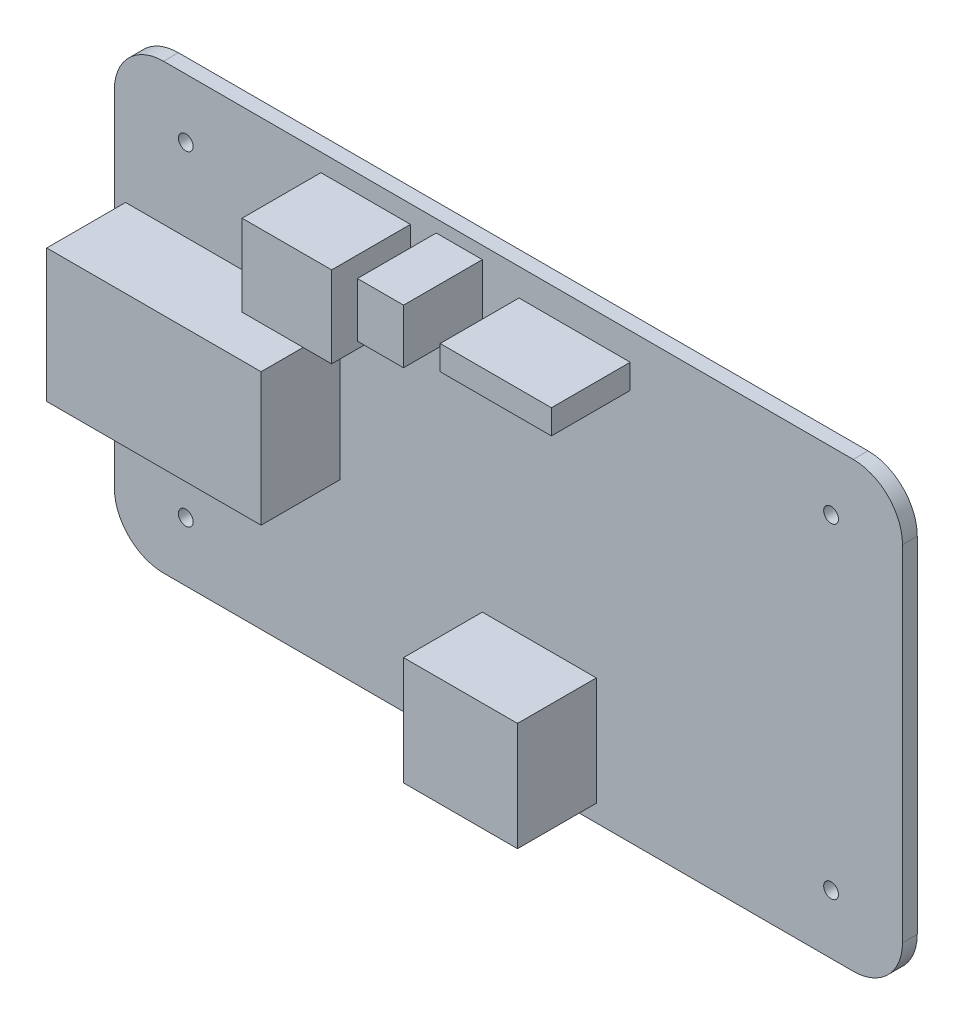
SolidWorks part; units mm, degrees
ref_plane "Front Plane" through (0, 0, 0) normal (0, 0, 1) x (1, 0, 0)
ref_plane "Top Plane" through (0, 0, 0) normal (0, 1, 0) x (1, 0, 0)
ref_plane "Right Plane" through (0, 0, 0) normal (1, 0, 0) x (0, 0, -1)
sketch "Sketch1" plane through (0, 0, 0) normal (0, 0, 1) x (1, 0, 0)
  line L1 (-80, 45) -> (80, 45)
  line L2 (-80, 45) -> (-80, -45)
  line L3 (-80, -45) -> (80, -45)
  line L4 (80, 45) -> (80, -45)
  line L5 (-80, 45) -> (80, -45) construction
  line L6 (-80, -45) -> (80, 45) construction
  point P0 (0, 0)
  dimension "D1" = 90
  dimension "D2" = 160
extrude "Boss-Extrude1" add sketch "Sketch1" along normal blind 3
fillet "Fillet1" radius 10 4 edges at (-80, -45, 1.5) (80, -45, 1.5) (80, 45, 1.5) (-80, 45, 1.5)
sketch "Sketch2" plane through (0, 0, 3) normal (0, 0, 1) x (1, 0, 0)
  line L5 (-65.5, 33) -> (65.5, -33) construction
  line L6 (-65.5, -33) -> (65.5, 33) construction
  circle A0 centre (-65.5, 33) radius 1.5
  circle A1 centre (65.5, 33) radius 1.5
  circle A2 centre (65.5, -33) radius 1.5
  circle A3 centre (-65.5, -33) radius 1.5
  point P0 (0, 0)
  dimension "D3" = 3
  dimension "D4" = 3
  dimension "D5" = 3
  dimension "D6" = 3
  dimension "D1" = 131
  dimension "D2" = 66
extrude "Cut-Extrude1" cut sketch "Sketch2" against normal through all
sketch "Sketch3" plane through (0, 0, 3) normal (0, 0, 1) x (1, 0, 0)
  line L1 (-77.7255, 16.3109) -> (-34.2096, 16.3109)
  line L2 (-77.7255, 16.3109) -> (-77.7255, -10.68)
  line L3 (-77.7255, -10.68) -> (-34.2096, -10.68)
  line L4 (-34.2096, 16.3109) -> (-34.2096, -10.68)
  line L5 (-77.7255, 16.3109) -> (-34.2096, -10.68) construction
  line L6 (-77.7255, -10.68) -> (-34.2096, 16.3109) construction
  line L7 (-5.2908, -19.4933) -> (17.8443, -19.4933)
  line L8 (-5.2908, -19.4933) -> (-5.2908, -41.5267)
  line L9 (-5.2908, -41.5267) -> (17.8443, -41.5267)
  line L10 (17.8443, -19.4933) -> (17.8443, -41.5267)
  line L11 (-5.2908, -19.4933) -> (17.8443, -41.5267) construction
  line L12 (-5.2908, -41.5267) -> (17.8443, -19.4933) construction
  line L13 (-38.0654, 41.3739) -> (-19.8879, 41.3739)
  line L14 (-38.0654, 41.3739) -> (-38.0654, 24.8489)
  line L15 (-38.0654, 24.8489) -> (-19.8879, 24.8489)
  line L16 (-19.8879, 41.3739) -> (-19.8879, 24.8489)
  line L17 (-38.0654, 41.3739) -> (-19.8879, 24.8489) construction
  line L18 (-38.0654, 24.8489) -> (-19.8879, 41.3739) construction
  line L19 (-14.655, 42.4756) -> (-5.2908, 42.4756)
  line L20 (-14.655, 42.4756) -> (-14.655, 31.4589)
  line L21 (-14.655, 31.4589) -> (-5.2908, 31.4589)
  line L22 (-5.2908, 42.4756) -> (-5.2908, 31.4589)
  line L23 (-14.655, 42.4756) -> (-5.2908, 31.4589) construction
  line L24 (-14.655, 31.4589) -> (-5.2908, 42.4756) construction
  line L25 (2.1455, 34.4885) -> (24.7297, 34.4885)
  line L26 (2.1455, 34.4885) -> (2.1455, 39.446)
  line L27 (2.1455, 39.446) -> (24.7297, 39.446)
  line L28 (24.7297, 34.4885) -> (24.7297, 39.446)
  line L29 (2.1455, 34.4885) -> (24.7297, 39.446) construction
  line L30 (2.1455, 39.446) -> (24.7297, 34.4885) construction
  point P0 (-55.9675, 2.8155)
  point P5 (6.2767, -30.51)
  point P10 (-28.9767, 33.1114)
  point P15 (-9.9729, 36.9672)
  point P20 (13.4376, 36.9672)
extrude "Boss-Extrude2" add sketch "Sketch3" along normal blind 16
